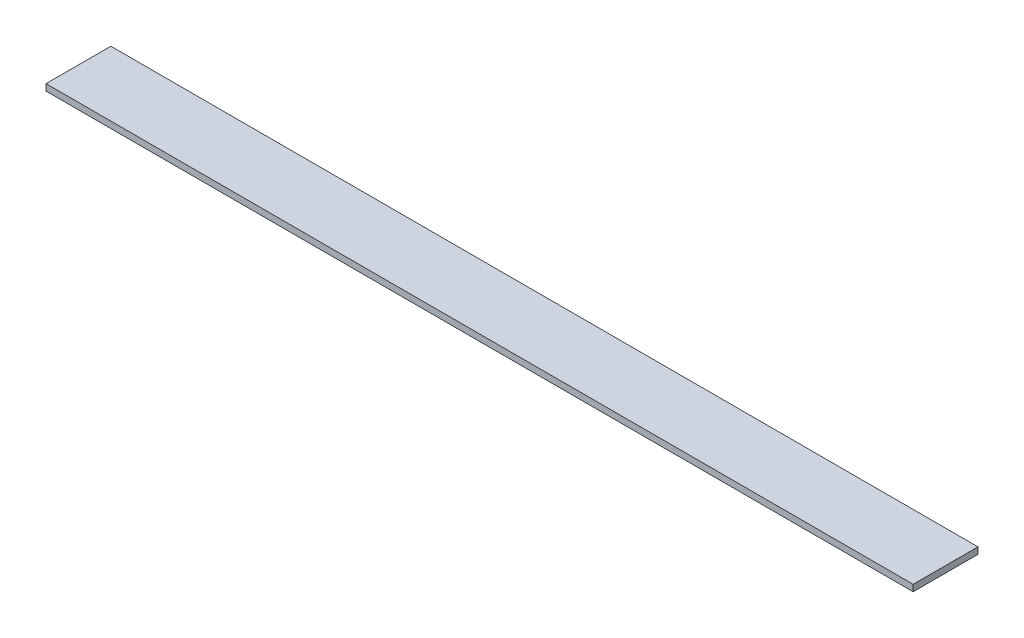
SolidWorks part; units mm, degrees
ref_plane "Спереди" through (0, 0, 0) normal (0, 0, 1) x (1, 0, 0)
ref_plane "Сверху" through (0, 0, 0) normal (0, 1, 0) x (1, 0, 0)
ref_plane "Справа" through (0, 0, 0) normal (1, 0, 0) x (0, 0, -1)
sketch "Эскиз1" plane through (0, 0, 0) normal (1, 0, 0) x (0, 0, -1)
  line L1 (-40, 0) -> (40, 0)
  line L2 (-40, 0) -> (-40, 8)
  line L3 (-40, 8) -> (40, 8)
  line L4 (40, 0) -> (40, 8)
  point P4 (0, 0)
extrude "Бобышка-Вытянуть1" add sketch "Эскиз1" along normal blind 1070
